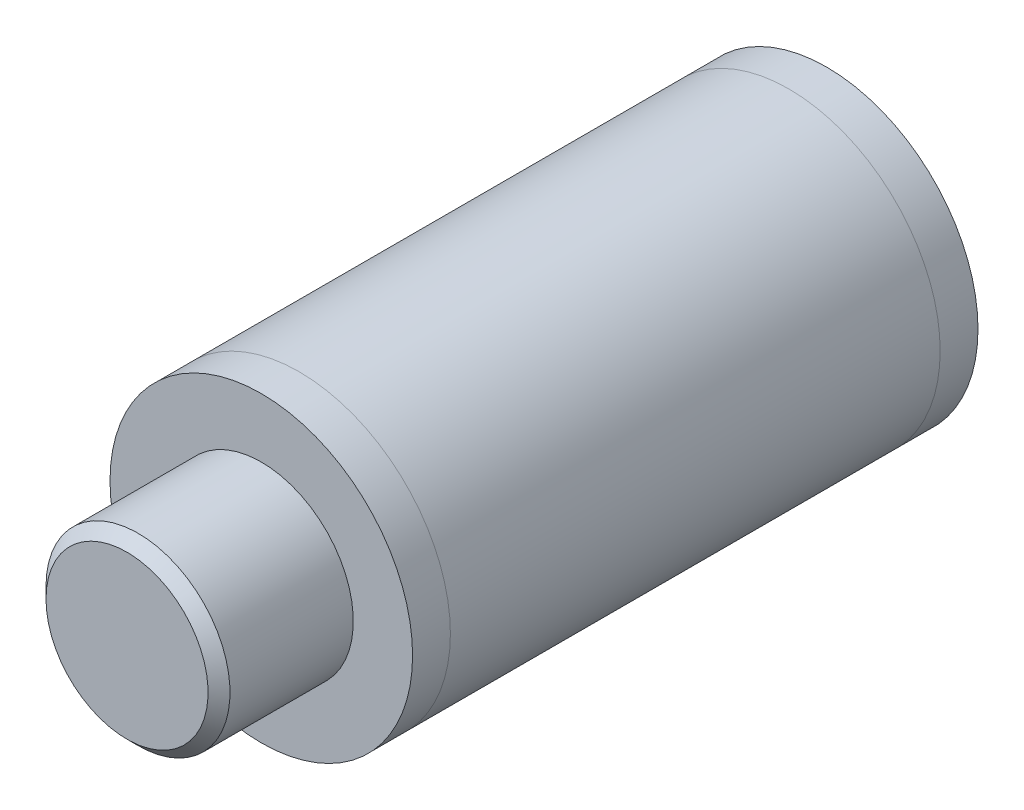
SolidWorks part; units mm, degrees
ref_plane "Front Plane" through (0, 0, 0) normal (0, 0, 1) x (1, 0, 0)
ref_plane "Top Plane" through (0, 0, 0) normal (0, 1, 0) x (1, 0, 0)
ref_plane "Right Plane" through (0, 0, 0) normal (1, 0, 0) x (0, 0, -1)
ref_plane "Plane1" through (0, 0, 0) normal (0, 1, 0) x (-1, 0, 0)
sketch "Sketch1" plane through (0, 0, 0) normal (0, 1, 0) x (-1, 0, 0)
  line L0 (0, 0) -> (-8, 0)
  line L1 (-8, 0) -> (-8, 29.9)
  line L2 (-8, 29.9) -> (0, 29.9)
  line L3 (0, 29.9) -> (0, 0)
  line L4 (0, 29.9) -> (0, 0) construction
revolve "Revolve1" add sketch "Sketch1" angle 360 about L4
ref_plane "Plane2" through (0, 0, 0) normal (0, 1, 0) x (-1, 0, 0)
sketch "Sketch2" plane through (0, 0, 0) normal (0, 1, 0) x (-1, 0, 0)
  line L0 (0, 29.9) -> (-4.865, 29.9)
  line L1 (-4.865, 29.9) -> (-4.865, 36.42)
  line L2 (-4.865, 36.42) -> (-4.285, 37)
  line L3 (-4.285, 37) -> (0, 37)
  line L4 (0, 37) -> (0, 29.9)
  line L5 (0, 37) -> (0, 29.9) construction
revolve "Revolve2" add sketch "Sketch2" angle 360 about L5
cosmetic thread "Cosmetic Thread1" parameters "D1"=6.6, "D2"=8.57
ref_plane "Plane3" through (0, 0, 27.9) normal (0, 0, 1) x (1, 0, 0)
ref_plane "Plane4" through (0, 0, 2) normal (0, 0, -1) x (-1, 0, 0)
split line "Split Line1"
split line "Split Line2"
